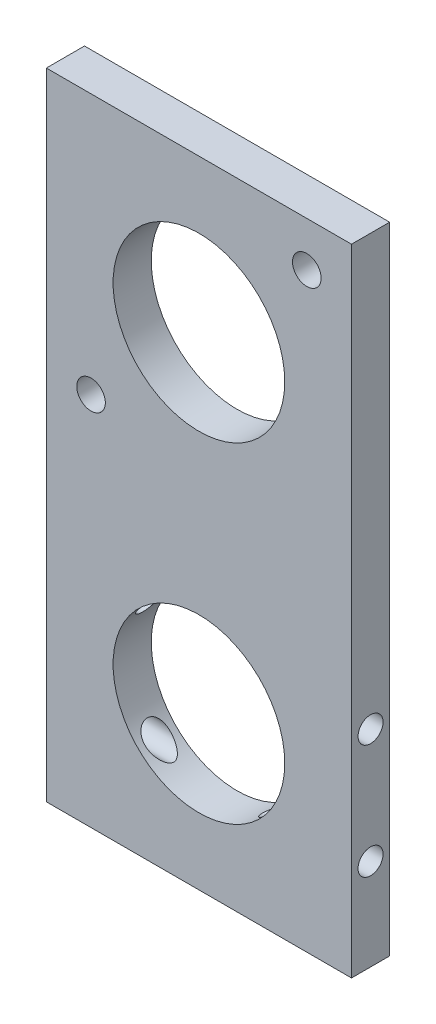
SolidWorks part; units mm, degrees
ref_plane "Front Plane" through (0, 0, 0) normal (0, 0, 1) x (1, 0, 0)
ref_plane "Top Plane" through (0, 0, 0) normal (0, 1, 0) x (1, 0, 0)
ref_plane "Right Plane" through (0, 0, 0) normal (1, 0, 0) x (0, 0, -1)
sketch "Sketch2" plane through (0, 0, 0) normal (0, 0, 1) x (1, 0, 0)
  line L0 (0, -25.4) -> (0, -29.6) construction
  line L3 (25.4, -80.4) -> (-25.4, -80.4)
  line L27 (25.4, 25.4) -> (-25.4, 25.4)
  line L28 (-25.4, 25.4) -> (-25.4, -80.4)
  line L29 (25.4, 25.4) -> (25.4, -80.4)
  line L30 (17.9605, 17.9605) -> (-17.9605, -17.9605) construction
  line L31 (0, 25.4) -> (0, -80.4) construction
  circle A7 centre (0, 0) radius 14.2875
  circle A12 centre (0, -55) radius 14.2875
  circle A15 centre (-17.9605, -17.9605) radius 2.3812
  circle A19 centre (17.9605, 17.9605) radius 2.3813
  circle A30 centre (0, -55) radius 25.4 construction
  circle A31 centre (0, 0) radius 25.4 construction
  point P4 (0, -27.5)
  point P11 (0, -80.4)
  point P14 (0, 25.4)
  point P16 (0, 0)
  dimension "D3" = 28.575
  dimension "D5" = 50.8
  dimension "D2" = 4.7625
  dimension "D7" = 28.575
  dimension "D6" = 55
  dimension "D1" = 50.8
  dimension "D4" = 45
extrude "Boss-Extrude1" add sketch "Sketch2" along normal blind 6.35
sketch "Sketch6" plane through (25.4, 0, 0) normal (1, 0, 0) x (0, 0, -1)
  line L0 (-3.175, -80.4) -> (-3.175, 25.4) construction
  line L1 (-6.35, -80.4) -> (0, -80.4) construction
  line L2 (-6.35, 25.4) -> (0, 25.4) construction
  circle A0 centre (-3.175, -65.16) radius 2.0828
  circle A1 centre (-3.175, -46.11) radius 2.0828
  dimension "D2" = 4.1656
  dimension "D3" = 15.24
  dimension "D1" = 19.05
extrude "Cut-Extrude1" cut sketch "Sketch6" against normal through all
equation "\"Pulley Teeth\"= 24"
equation "\"Belt Teeth\"= 46"
equation "\"Leftover Teeth\"= \"Belt Teeth\" - \"Pulley Teeth\""
equation "\"teeth size\"= 5mm"
equation "\"length\"= ( \"Leftover Teeth\" * \"teeth size\" ) / 2"
equation "\"D6@Sketch2\"=\"length\""
equation "\"belt size\"= ( \"Belt Teeth\" * \"teeth size\" )"
equation "\"belrt size\"= 220mm"
equation "\"blt\"= \"belrt size\" / \"teeth size\""
